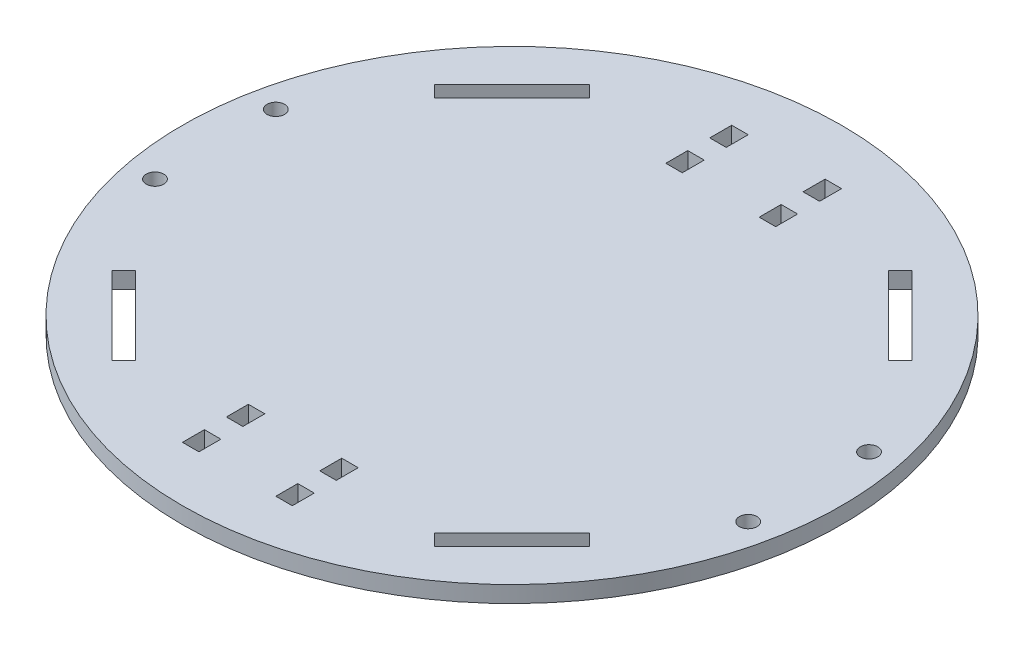
SolidWorks part; units mm, degrees
material "Acrylic (Medium-high impact)"
ref_plane "Plano frontal," through (0, 0, 0) normal (0, 0, 1) x (1, 0, 0)
ref_plane "Plano superior" through (0, 0, 0) normal (0, 1, 0) x (1, 0, 0)
ref_plane "Plano direito" through (0, 0, 0) normal (1, 0, 0) x (0, 0, -1)
sketch "Sketch1" plane through (0, 0, 0) normal (0, 1, 0) x (1, 0, 0)
  circle A0 centre (0, 0) radius 60
  dimension "D1" = 120
extrude "Boss-Extrude1" add sketch "Sketch1" along normal mid plane 3
sketch "Sketch2" plane through (0, 0, 0) normal (0, 1, 0) x (1, 0, 0)
  circle A0 centre (54, 11) radius 1.6
  circle A1 centre (0, 0) radius 60 construction
  point P6 (58.9107, 11.381)
  dimension "D1" = 3.2
  dimension "D2" = 11
  dimension "D3" = 54
extrude "Cut-Extrude1" cut sketch "Sketch2" against normal through all both and the other way through all
mirror "Mirror1" about plane through (0, 0, 0) normal (1, 0, 0) of "Cut-Extrude1"
mirror "Mirror2" about plane through (0, 0, 0) normal (0, 0, 1) of "Cut-Extrude1", "Mirror1"
sketch "Sketch3" plane through (0, 1.5, 0) normal (0, 1, 0) x (1, 0, 0)
  line L1 (-10, 50) -> (-7, 50)
  line L2 (-10, 50) -> (-10, 46)
  line L3 (-10, 46) -> (-7, 46)
  line L4 (-7, 50) -> (-7, 46)
  line L5 (-10, 50) -> (-7, 46) construction
  line L6 (-10, 46) -> (-7, 50) construction
  circle A0 centre (0, 0) radius 60 construction
  point P0 (-8.5, 48)
  dimension "D1" = 7
  dimension "D2" = 3
  dimension "D3" = 4
  dimension "D4" = 50
extrude "Cut-Extrude2" cut sketch "Sketch3" against normal through all
pattern_linear "LPattern1" count 2 spacing 8 along (0, 0, 1) of "Cut-Extrude2"
mirror "Mirror3" about plane through (0, 0, 0) normal (1, 0, 0) of "LPattern1", "Cut-Extrude2"
mirror "Mirror4" about plane through (0, 0, 0) normal (0, 0, 1) of "Mirror3", "LPattern1", "Cut-Extrude2"
sketch "Sketch4" plane through (0, 1.5, 0) normal (0, 1, 0) x (1, 0, 0)
  line L0 (27.2236, 41.3657) -> (41.3657, 27.2236)
  line L1 (27.2236, 41.3657) -> (29.3449, 43.4871)
  line L2 (41.3657, 27.2236) -> (43.4871, 29.3449)
  line L3 (29.3449, 43.4871) -> (43.4871, 29.3449)
  line L4 (27.2236, 41.3657) -> (43.4871, 29.3449) construction
  line L5 (41.3657, 27.2236) -> (29.3449, 43.4871) construction
  line L6 (0, 0) -> (35.3553, 35.3553) construction
  point P1 (35.3553, 35.3553)
  dimension "D1" = 3
  dimension "D2" = 20
  dimension "D3" = 50
  dimension "D4" = 45
extrude "Cut-Extrude3" cut sketch "Sketch4" against normal through all both and the other way through all
pattern_circular "CirPattern1" count 4 over 360 about axis through (0, 0, 0) along (0, 1, 0) of "Cut-Extrude3"
